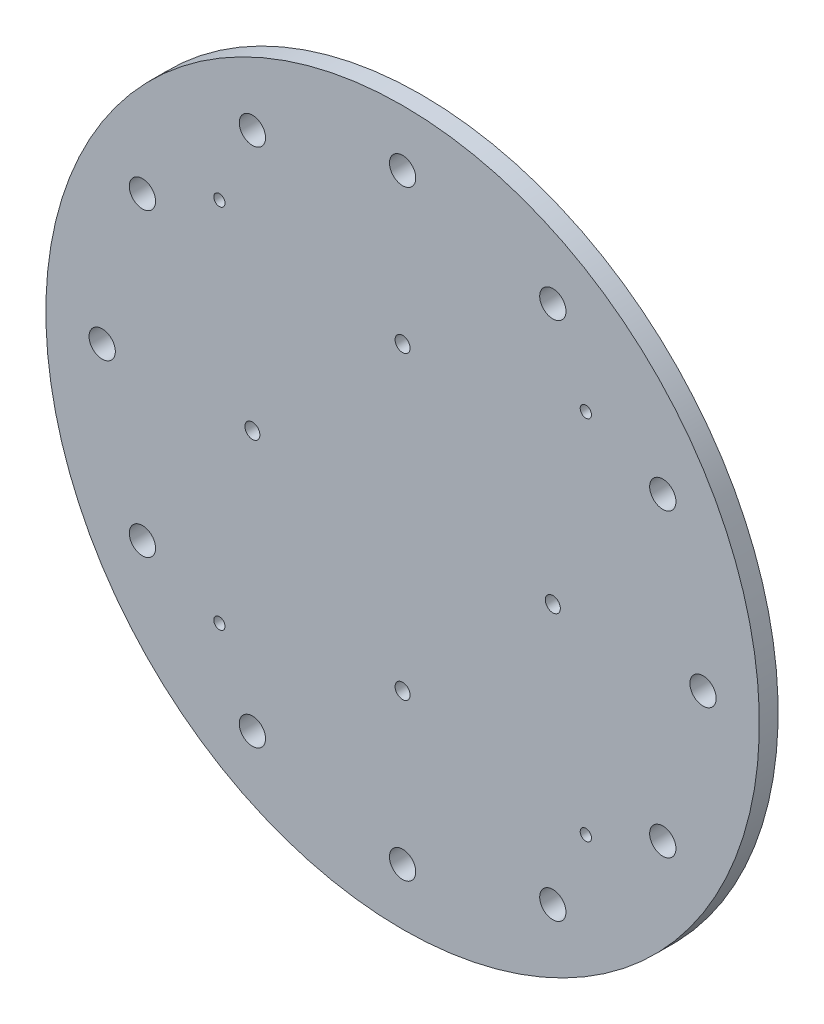
SolidWorks part; units mm, degrees
ref_plane "Front Plane" through (0, 0, 0) normal (0, 0, 1) x (1, 0, 0)
ref_plane "Top Plane" through (0, 0, 0) normal (0, 1, 0) x (1, 0, 0)
ref_plane "Right Plane" through (0, 0, 0) normal (1, 0, 0) x (0, 0, -1)
sketch "Sketch1" plane through (0, 0, 0) normal (0, 1, 0) x (1, 0, 0)
  line L0 (0, 0) -> (69, 0) construction
  line L1 (0, 0) -> (48.7904, 48.7904) construction
  line L12 (0, 0) -> (0, 40) construction
  line L13 (69, 0) -> (80, 0) construction
  circle A6 centre (0, 0) radius 69 construction
  circle A8 centre (48.7904, 48.7904) radius 1.5
  circle A21 centre (0, 0) radius 40 construction
  circle A22 centre (0, 40) radius 2
  circle A23 centre (0, 0) radius 40 construction
  circle A24 centre (40, 0) radius 2
  circle A25 centre (0, 0) radius 40 construction
  circle A26 centre (0, -40) radius 2
  circle A27 centre (0, 0) radius 40 construction
  circle A28 centre (-40, 0) radius 2
  circle A42 centre (0, 0) radius 69 construction
  circle A43 centre (48.7904, -48.7904) radius 1.5
  circle A44 centre (0, 0) radius 69 construction
  circle A48 centre (-48.7904, -48.7904) radius 1.5
  circle A49 centre (0, 0) radius 69 construction
  circle A52 centre (-48.7904, 48.7904) radius 1.5
  circle A53 centre (0, 0) radius 95
  circle A55 centre (0, 0) radius 80 construction
  circle A61 centre (80, 0) radius 3.5
  circle A62 centre (0, 0) radius 80 construction
  circle A63 centre (69.282, -40) radius 3.5
  circle A64 centre (0, 0) radius 80 construction
  circle A65 centre (40, -69.282) radius 3.5
  circle A66 centre (0, 0) radius 80 construction
  circle A67 centre (0, -80) radius 3.5
  circle A68 centre (0, 0) radius 80 construction
  circle A69 centre (-40, -69.282) radius 3.5
  circle A70 centre (0, 0) radius 80 construction
  circle A71 centre (-69.282, -40) radius 3.5
  circle A72 centre (0, 0) radius 80 construction
  circle A73 centre (-80, 0) radius 3.5
  circle A74 centre (0, 0) radius 80 construction
  circle A75 centre (-69.282, 40) radius 3.5
  circle A76 centre (0, 0) radius 80 construction
  circle A77 centre (-40, 69.282) radius 3.5
  circle A78 centre (0, 0) radius 80 construction
  circle A79 centre (0, 80) radius 3.5
  circle A80 centre (0, 0) radius 80 construction
  circle A81 centre (40, 69.282) radius 3.5
  circle A82 centre (0, 0) radius 80 construction
  circle A83 centre (69.282, 40) radius 3.5
  dimension "D4" = 138
  dimension "D5" = 45
  dimension "D15" = 80
  dimension "D16" = 4
  dimension "D10" = 160
  dimension "D7" = 3
  dimension "D8" = 4
  dimension "D9" = 190
  dimension "D11" = 7
  dimension "D17" = 4
  dimension "D34" = 12
extrude "Boss-Extrude1" add sketch "Sketch1" along normal blind 5
move or copy body "Body-Move/Copy1" bodies to move or copy 101 copy no rotation origin (0, 2.5, 0) rotation axis (1, 0, 0) rotation angle 90
